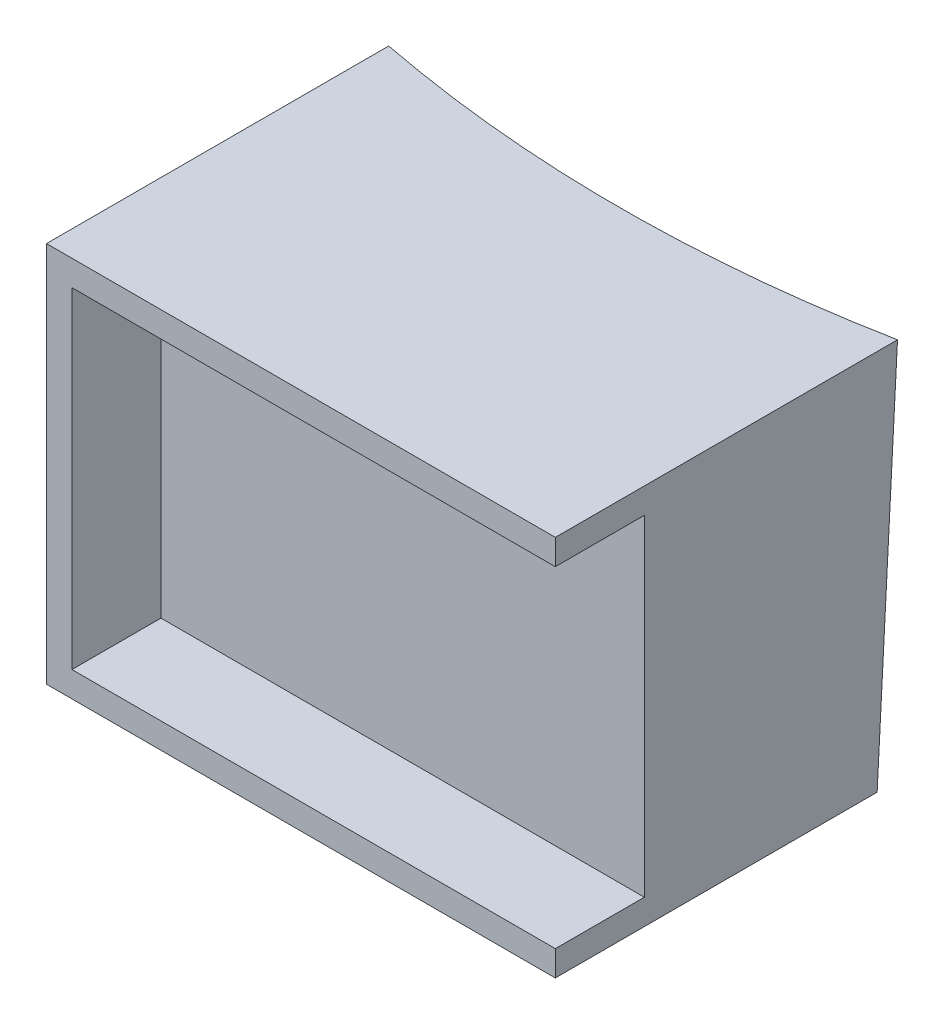
SolidWorks part; units mm, degrees
ref_plane "Front Plane" through (0, 0, 0) normal (0, 0, 1) x (1, 0, 0)
ref_plane "Top Plane" through (0, 0, 0) normal (0, 1, 0) x (1, 0, 0)
ref_plane "Right Plane" through (0, 0, 0) normal (1, 0, 0) x (0, 0, -1)
sketch "Sketch1" plane through (0, 0, 0) normal (0, 0, 1) x (1, 0, 0)
  line L1 (0, 30) -> (40, 30)
  line L2 (0, 30) -> (0, 0)
  line L3 (0, 0) -> (40, 0)
  line L4 (40, 30) -> (40, 0)
  point P4 (0, 0)
  dimension "D1" = 40
  dimension "D2" = 30
extrude "Boss-Extrude1" add sketch "Sketch1" along normal blind 130
sketch "Sketch2" plane through (0, 0, 0) normal (0, 0, -1) x (-1, 0, 0)
  line L0 (-20, 30) -> (-20, 0) construction
  line L1 (-40, 30) -> (0, 30) construction
  line L2 (0, 0) -> (-40, 0) construction
sketch "Sketch3" plane through (0, 0, 130) normal (0, 0, 1) x (1, 0, 0)
  line L0 (20, 30) -> (20, 0) construction
  line L1 (0, 0) -> (40, 0) construction
ref_plane "Plane1" through (20, 0, 0) normal (1, 0, 0) x (0, 0, -1)
sketch "Sketch4" plane through (20, 0, 0) normal (1, 0, 0) x (0, 0, -1)
  line L0 (0, 60) -> (0, -170)
  line L1 (0, 60) -> (-103.45, 60)
  line L2 (-103.45, 60) -> (-115.5038, -170)
  line L3 (-115.5038, -170) -> (0, -170)
  line L4 (-130, 0) -> (0, 0) construction
  point P7 (-129.4019, -170)
  dimension "D1" = 230
  dimension "D2" = 103.45
  dimension "D3" = 60
  dimension "D4" = 93
revolve "Cut-Revolve1" cut sketch "Sketch4" angle 360 about L0
ref_plane "Plane2" through (0, 0, 120) normal (0, 0, 1) x (1, 0, 0)
sketch "Sketch6" plane through (0, 0, 120) normal (0, 0, 1) x (1, 0, 0)
  line L0 (0, 30) -> (0, 0) construction
  line L1 (5, 25) -> (35, 25)
  line L2 (5, 25) -> (5, 5)
  line L3 (5, 5) -> (35, 5)
  line L4 (35, 25) -> (35, 5)
  line L5 (40, 30) -> (0, 30) construction
  line L7 (40, 0) -> (40, 30) construction
  line L8 (0, 0) -> (40, 0) construction
  dimension "D1" = 5
  dimension "D2" = 5
  dimension "D3" = 5
  dimension "D4" = 5
extrude "Cut-Extrude1" cut sketch "Sketch6" against normal blind 10 contours L2 L1 L4 L3
sketch "Sketch7" plane through (0, 0, 130) normal (0, 0, 1) x (1, 0, 0)
  line L0 (40, 0) -> (40, 30) construction
  line L1 (40, 28) -> (2, 28)
  line L2 (40, 28) -> (40, 2)
  line L3 (40, 2) -> (2, 2)
  line L4 (2, 28) -> (2, 2)
  line L5 (40, 30) -> (0, 30) construction
  line L6 (0, 30) -> (0, 0) construction
  dimension "D1" = 26
  dimension "D2" = 2
  dimension "D3" = 2
extrude "Cut-Extrude2" cut sketch "Sketch7" against normal blind 7
